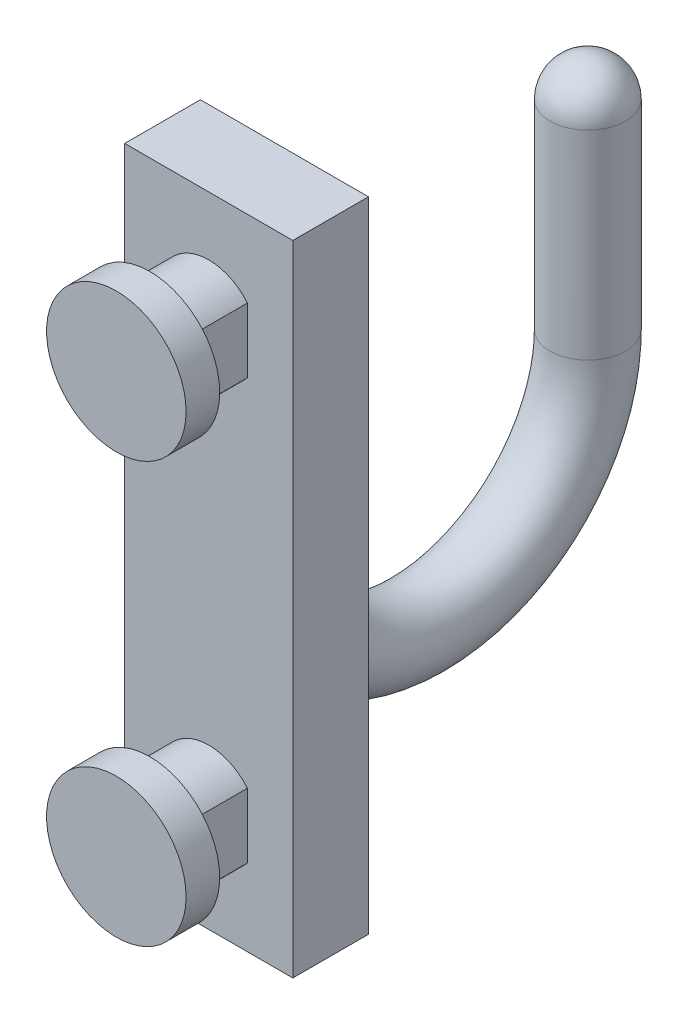
SolidWorks part; units mm, degrees
ref_plane "Front Plane" through (0, 0, 0) normal (0, 0, 1) x (1, 0, 0)
ref_plane "Top Plane" through (0, 0, 0) normal (0, 1, 0) x (1, 0, 0)
ref_plane "Right Plane" through (0, 0, 0) normal (1, 0, 0) x (0, 0, -1)
sketch "草图1" plane through (0, 0, 0) normal (0, 0, 1) x (1, 0, 0)
  line L0 (-2.3, 1.9261) -> (-2.3, -1.9261)
  line L3 (2.3, 1.9261) -> (2.3, -1.9261)
  line L4 (-2.3, -23.0739) -> (-2.3, -26.9261)
  line L5 (2.3, -23.0739) -> (2.3, -26.9261)
  arc A0 (-2.3, -1.9261) -> (2.3, -1.9261) centre (0, 0) ccw
  arc A1 (2.3, 1.9261) -> (-2.3, 1.9261) centre (0, 0) ccw
  arc A2 (-2.3, -26.9261) -> (2.3, -26.9261) centre (0, -25) ccw
  arc A3 (2.3, -23.0739) -> (-2.3, -23.0739) centre (0, -25) ccw
  dimension "D1" = 3
  dimension "D4" = 3
  dimension "D2" = 4.6
  dimension "D3" = 4.6
  dimension "D5" = 25
  dimension "D6" = 2.3
  dimension "D7" = 2.3
extrude "凸台-拉伸1" add sketch "草图1" along normal blind 3.5
sketch "草图2" plane through (0, 0, 3.5) normal (0, 0, 1) x (1, 0, 0)
  circle A0 centre (0, 0) radius 4.15
  circle A1 centre (0, -25) radius 4.15
  arc A2 (2.3, -23.0739) -> (-2.3, -23.0739) centre (0, -25) ccw construction
  dimension "D1" = 8.3
  dimension "D2" = 8.3
extrude "凸台-拉伸2" add sketch "草图2" along normal blind 2
sketch "草图3" plane through (0, 0, 0) normal (0, 0, -1) x (-1, 0, 0)
  line L1 (-5, 6.5) -> (5, 6.5)
  line L2 (-5, 6.5) -> (-5, -31.5)
  line L3 (-5, -31.5) -> (5, -31.5)
  line L4 (5, 6.5) -> (5, -31.5)
  dimension "D1" = 38
  dimension "D2" = 10
  dimension "D3" = 5
  dimension "D4" = 6.5
extrude "凸台-拉伸3" add sketch "草图3" along normal blind 4.5
sketch "草图4" plane through (0, 0, 0) normal (1, 0, 0) x (0, 0, -1)
  line L0 (2.25, 0) -> (2.25, -11.85)
  line L5 (22.55, -11.85) -> (22.55, 0)
  arc A0 (2.25, -11.85) -> (22.55, -11.85) centre (12.4, -11.85) ccw
  dimension "D3" = 10.15
  dimension "D1" = 2.25
ref_plane "基准面1" through (0, 0, 0) normal (0, 1, 0) x (1, 0, 0)
sketch "草图5" plane through (0, 0, 0) normal (0, 1, 0) x (1, 0, 0)
  circle A0 centre (0, 22.55) radius 2.25
  dimension "D1" = 4.5
sweep "扫描1" add profiles "草图5" path "草图4"
sketch "草图6" plane through (0, 0, 0) normal (1, 0, 0) x (0, 0, -1)
  line L0 (22.55, 0) -> (22.55, 2.25)
  line L1 (22.55, 0) -> (20.3, 0)
  arc A0 (20.3, 0) -> (22.55, 2.25) centre (22.55, 0) cw
revolve "旋转1" add sketch "草图6" angle 360 about L0
